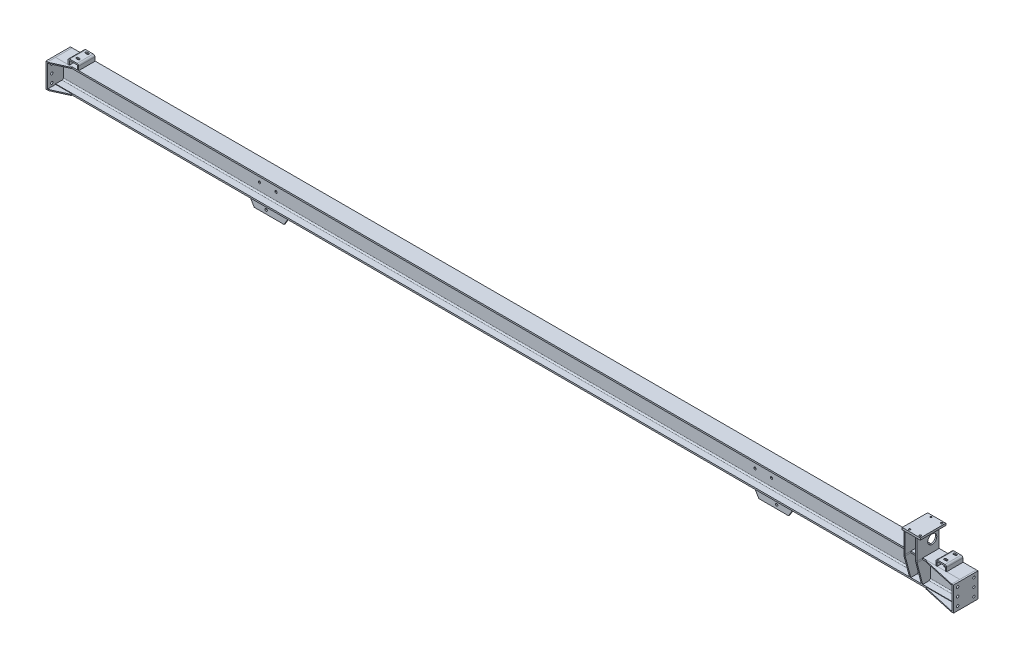
SolidWorks part; units mm, degrees
material "普通碳钢"
ref_plane "前视基准面" through (0, 0, 0) normal (0, 0, 1) x (1, 0, 0)
ref_plane "上视基准面" through (0, 0, 0) normal (0, 1, 0) x (1, 0, 0)
ref_plane "右视基准面" through (0, 0, 0) normal (1, 0, 0) x (0, 0, -1)
sketch "草图17" plane through (0, -1296.9389, 0) normal (0, 0, 1) x (1, 0, 0)
  line L0 (4200.9132, -4872.6106) -> (-1274.0868, -4872.6106)
  dimension "D1" = 5475
other "H型钢 HM150×100(3)"
ref_plane "基准面7" through (4200.9132, -6243.5496, 50) normal (-1, 0, 0) x (0, 0, 1)
sketch "草图1" plane through (4200.9132, -6243.5496, 50) normal (-1, 0, 0) x (0, 0, 1)
  line L0 (-50, -74) -> (50, -74)
  line L1 (50, -74) -> (50, -65)
  line L2 (50, -65) -> (11, -65)
  line L3 (3, -57) -> (3, 57)
  line L4 (11, 65) -> (50, 65)
  line L5 (50, 65) -> (50, 74)
  line L6 (50, 74) -> (-50, 74)
  line L7 (0, 74) -> (0, -74) construction
  line L11 (0, 60) -> (0, 74) construction
  line L14 (-50, -74) -> (-50, -65)
  line L15 (-50, -65) -> (-11, -65)
  line L16 (-3, -57) -> (-3, 57)
  line L17 (-11, 65) -> (-50, 65)
  line L18 (-50, 65) -> (-50, 74)
  arc A2 (11, -65) -> (3, -57) centre (11, -57) cw
  arc A3 (3, 57) -> (11, 65) centre (11, 57) cw
  arc A5 (-11, -65) -> (-3, -57) centre (-11, -57) ccw
  arc A6 (-3, 57) -> (-11, 65) centre (-11, 57) ccw
  point P2 (0, 0)
  point P38 (0, 0)
  point P39 (50, 74)
  point P40 (50, -74)
  point P41 (-50, -74)
  dimension "D8" = 8
  dimension "D1" = 6
  dimension "D2" = 9
  dimension "D3" = 148
  dimension "D4" = 100
  dimension "D9" = 0
sketch "草图18" plane through (4200.9132, 0, 0) normal (1, 0, 0) x (0, 0, -1)
  line L0 (0, -6317.5496) -> (-100, -6317.5496) construction
  line L1 (0, -6169.5496) -> (-148, -6169.5496)
  line L2 (0, -6169.5496) -> (0, -6317.5496)
  line L3 (0, -6317.5496) -> (-148, -6317.5496)
  line L4 (-148, -6169.5496) -> (-148, -6317.5496)
  dimension "D1" = 148
extrude "凸台-拉伸1" add sketch "草图18" along normal blind 10 separate body contours L1 L4 L3 L2
sketch "草图19" plane through (-1274.0868, 0, 0) normal (-1, 0, 0) x (0, 0, 1)
  line L0 (0, -6317.5496) -> (100, -6317.5496) construction
  line L1 (0, -6169.5496) -> (148, -6169.5496)
  line L2 (0, -6169.5496) -> (0, -6317.5496)
  line L3 (0, -6317.5496) -> (148, -6317.5496)
  line L4 (148, -6169.5496) -> (148, -6317.5496)
  dimension "D1" = 148
extrude "凸台-拉伸2" add sketch "草图19" along normal blind 10 separate body
sketch "草图20" plane through (0, -6169.5496, 0) normal (0, 1, 0) x (1, 0, 0)
  line L0 (-1274.0868, -100) -> (-1274.0868, -148)
  line L1 (-1274.0868, -148) -> (-1269.0868, -148)
  line L2 (-1269.0868, -148) -> (-1174.0868, -105)
  line L3 (-1174.0868, -105) -> (-1174.0868, -100)
  line L4 (-1274.0868, -100) -> (4200.9132, -100) construction
  line L5 (-1174.0868, -100) -> (-1274.0868, -100)
  dimension "D1" = 5
  dimension "D2" = 5
  dimension "D3" = 100
extrude "凸台-拉伸3" add sketch "草图20" against normal blind 6 separate body contours L2 L3 L5 L0 L1
sketch "草图21" plane through (0, -6317.5496, 0) normal (0, -1, 0) x (1, 0, 0)
  line L5 (-1269.0868, 148) -> (-1274.0868, 148)
  line L6 (-1274.0868, 148) -> (-1274.0868, 100)
  line L7 (-1274.0868, 100) -> (-1174.0868, 100)
  line L8 (-1174.0868, 100) -> (-1174.0868, 105)
  line L9 (-1174.0868, 105) -> (-1269.0868, 148)
  line L10 (-1269.0868, 148) -> (-1274.0868, 148)
  line L11 (-1274.0868, 148) -> (-1274.0868, 100)
  line L12 (-1274.0868, 100) -> (-1174.0868, 100)
  line L13 (-1174.0868, 100) -> (-1174.0868, 105)
  line L14 (-1174.0868, 105) -> (-1269.0868, 148)
  dimension "D1" = 0
extrude "凸台-拉伸4" add sketch "草图21" against normal blind 6 separate body
sketch "草图22" plane through (0, -6169.5496, 0) normal (0, 1, 0) x (1, 0, 0)
  line L0 (4200.9132, -100) -> (4200.9132, -148)
  line L1 (4200.9132, -148) -> (4195.9132, -148)
  line L2 (4195.9132, -148) -> (4000.9132, -105)
  line L3 (4000.9132, -105) -> (4000.9132, -100)
  line L4 (-1274.0868, -100) -> (4200.9132, -100) construction
  line L5 (4000.9132, -100) -> (4200.9132, -100)
  dimension "D1" = 200
  dimension "D2" = 5
  dimension "D3" = 5
extrude "凸台-拉伸5" add sketch "草图22" against normal blind 6 separate body contours L2 L3 L5 L0 L1
sketch "草图23" plane through (0, -6317.5496, 0) normal (0, -1, 0) x (1, 0, 0)
  line L5 (4200.9132, 148) -> (4195.9132, 148)
  line L6 (4195.9132, 148) -> (4000.9132, 105)
  line L7 (4000.9132, 105) -> (4000.9132, 100)
  line L8 (4000.9132, 100) -> (4200.9132, 100)
  line L9 (4200.9132, 100) -> (4200.9132, 148)
  line L10 (4200.9132, 148) -> (4195.9132, 148)
  line L11 (4195.9132, 148) -> (4000.9132, 105)
  line L12 (4000.9132, 105) -> (4000.9132, 100)
  line L13 (4000.9132, 100) -> (4200.9132, 100)
  line L14 (4200.9132, 100) -> (4200.9132, 148)
  dimension "D1" = 0
extrude "凸台-拉伸6" add sketch "草图23" against normal blind 6 separate body
sketch "草图24" plane through (-1284.0868, 0, 0) normal (-1, 0, 0) x (0, 0, 1)
  line L0 (0, -6242.5496) -> (148, -6242.5496) construction
  line L1 (0, -6169.5496) -> (0, -6317.5496) construction
  line L2 (148, -6317.5496) -> (148, -6169.5496) construction
  line L3 (0, -6192.5496) -> (148, -6192.5496) construction
  line L4 (0, -6292.5496) -> (148, -6292.5496) construction
  line L5 (25, -6169.5496) -> (25, -6317.5496) construction
  line L6 (148, -6169.5496) -> (0, -6169.5496) construction
  line L7 (0, -6317.5496) -> (148, -6317.5496) construction
  line L8 (123, -6169.5496) -> (123, -6317.5496) construction
  circle A0 centre (25, -6192.5496) radius 7
  circle A1 centre (123, -6192.5496) radius 7
  circle A2 centre (25, -6242.5496) radius 7
  circle A3 centre (123, -6242.5496) radius 7
  circle A4 centre (25, -6292.5496) radius 7
  circle A5 centre (123, -6292.5496) radius 7
  dimension "D5" = 14
  dimension "D1" = 50
  dimension "D2" = 50
  dimension "D3" = 25
  dimension "D4" = 25
  dimension "D6" = 25
extrude "切除-拉伸1" cut sketch "草图24" against normal up to next (10 mm away)
sketch "草图25" plane through (4210.9132, 0, 0) normal (1, 0, 0) x (0, 0, -1)
  line L0 (-148, -6242.5496) -> (0, -6242.5496) construction
  line L1 (-148, -6169.5496) -> (-148, -6317.5496) construction
  line L2 (0, -6169.5496) -> (0, -6317.5496) construction
  line L3 (-148, -6192.5496) -> (0, -6192.5496) construction
  line L4 (-148, -6292.5496) -> (0, -6292.5496) construction
  line L5 (-123, -6169.5496) -> (-123, -6317.5496) construction
  line L6 (0, -6169.5496) -> (-148, -6169.5496) construction
  line L7 (0, -6317.5496) -> (-148, -6317.5496) construction
  line L8 (-25, -6169.5496) -> (-25, -6317.5496) construction
  circle A0 centre (-123, -6192.5496) radius 7
  circle A1 centre (-25, -6192.5496) radius 7
  circle A2 centre (-123, -6242.5496) radius 7
  circle A3 centre (-25, -6242.5496) radius 7
  circle A4 centre (-123, -6292.5496) radius 7
  circle A5 centre (-25, -6292.5496) radius 7
  dimension "D5" = 14
  dimension "D1" = 25
  dimension "D2" = 25
  dimension "D3" = 50
  dimension "D4" = 50
  dimension "D6" = 25
extrude "切除-拉伸2" cut sketch "草图25" against normal up to next (10 mm away)
sketch "草图26" plane through (0, 0, 47) normal (0, 0, -1) x (-1, 0, 0)
  line L0 (-1463.4132, -6169.5496) -> (-1463.4132, -6909.0666) construction
  line L1 (-4200.9132, -6169.5496) -> (1274.0868, -6169.5496) construction
  line L2 (-2963.4132, -6169.5496) -> (-2963.4132, -6909.0666) construction
  line L3 (36.5868, -6169.5496) -> (36.5868, -6909.0666) construction
  line L4 (-3013.4132, -6169.5496) -> (-3013.4132, -6909.0666) construction
  line L5 (-2913.4132, -6169.5496) -> (-2913.4132, -6909.0666) construction
  line L6 (-13.4132, -6169.5496) -> (-13.4132, -6909.0666) construction
  line L7 (86.5868, -6169.5496) -> (86.5868, -6909.0666) construction
  line L10 (-4200.9132, -6254.5496) -> (1274.0868, -6254.5496) construction
  line L11 (-4200.9132, -6204.5496) -> (1274.0868, -6204.5496)
  line L12 (-4200.9132, -6204.5496) -> (1274.0868, -6204.5496) construction
  circle A0 centre (-3013.4132, -6204.5496) radius 7
  circle A1 centre (-2913.4132, -6204.5496) radius 7
  circle A2 centre (-13.4132, -6204.5496) radius 7
  circle A3 centre (86.5868, -6204.5496) radius 7
  circle A4 centre (-3013.4132, -6254.5496) radius 7
  circle A5 centre (-2913.4132, -6254.5496) radius 7
  circle A6 centre (-13.4132, -6254.5496) radius 7
  circle A7 centre (86.5868, -6254.5496) radius 7
  dimension "D8" = 14
  dimension "D1" = 1500
  dimension "D2" = 1500
  dimension "D3" = 50
  dimension "D4" = 50
  dimension "D5" = 50
  dimension "D6" = 50
  dimension "D7" = 35
  dimension "D9" = 50
extrude "切除-拉伸3" cut sketch "草图26" against normal up to next (6 mm away) and the other way through all
ref_plane "基准面8" through (0, -6039.5496, 0) normal (0, 1, 0) x (1, 0, 0)
sketch "草图27" plane through (0, -6039.5496, 0) normal (0, 1, 0) x (1, 0, 0)
  line L0 (4005.9132, -67) -> (3895.9132, -67) construction
  line L1 (4005.9132, 10) -> (3895.9132, 10)
  line L2 (4005.9132, 10) -> (4005.9132, -144)
  line L3 (4005.9132, -144) -> (3895.9132, -144)
  line L4 (3895.9132, 10) -> (3895.9132, -144)
  line L5 (3960.9132, -144) -> (3960.9132, 10) construction
  line L6 (3993.4132, -144) -> (3993.4132, 10) construction
  line L7 (3928.4132, -144) -> (3928.4132, 10) construction
  line L8 (4005.9132, -2) -> (3895.9132, -2) construction
  line L9 (4005.9132, -132) -> (3895.9132, -132) construction
  line L10 (4200.9132, 0) -> (-1274.0868, 0) construction
  line L11 (4200.9132, 0) -> (4200.9132, -148) construction
  circle A0 centre (3993.4132, -132) radius 5.5
  circle A1 centre (3928.4132, -132) radius 5.5
  circle A2 centre (3993.4132, -2) radius 5.5
  circle A3 centre (3928.4132, -2) radius 5.5
  dimension "D7" = 11
  dimension "D1" = 110
  dimension "D2" = 154
  dimension "D3" = 32.5
  dimension "D8" = 10
  dimension "D9" = 195
  dimension "D10" = 45
  dimension "D4" = 32.5
  dimension "D5" = 65
  dimension "D6" = 65
extrude "凸台-拉伸7" add sketch "草图27" along normal blind 12 separate body
sketch "草图29" plane through (0, -6039.5496, 0) normal (0, -1, 0) x (1, 0, 0)
  line L1 (3895.9132, 134) -> (3903.9132, 134)
  line L2 (3895.9132, 134) -> (3895.9132, 0)
  line L3 (3895.9132, 0) -> (3903.9132, 0)
  line L4 (3903.9132, 134) -> (3903.9132, 0)
  line L6 (3895.9132, -10) -> (3895.9132, 144) construction
  line L7 (3967.9132, 134) -> (3975.9132, 134)
  line L8 (3967.9132, 134) -> (3967.9132, 0)
  line L9 (3967.9132, 0) -> (3975.9132, 0)
  line L10 (3975.9132, 134) -> (3975.9132, 0)
  line L11 (4005.9132, -10) -> (3895.9132, -10) construction
  line L12 (3895.9132, 144) -> (4005.9132, 144) construction
  line L13 (4005.9132, 144) -> (4005.9132, -10) construction
  dimension "D1" = 8
  dimension "D2" = 8
  dimension "D3" = 10
  dimension "D4" = 10
  dimension "D5" = 30
extrude "凸台-拉伸8" add sketch "草图29" along normal up to surface (130 mm away) separate body up to face at (1463.4132, -6169.5496, 50)
sketch "草图30" plane through (0, -6169.5496, 0) normal (0, -1, 0) x (1, 0, 0)
  line L0 (-1274.0868, 100) -> (4200.9132, 100) construction
  line L1 (3975.9132, 0) -> (3975.9132, 134) construction
  line L2 (3967.9132, 134) -> (3967.9132, 0) construction
  line L3 (3903.9132, 0) -> (3903.9132, 134) construction
  line L4 (3903.9132, 134) -> (3895.9132, 134)
  line L5 (3895.9132, 134) -> (3895.9132, 0)
  line L6 (3895.9132, 0) -> (3903.9132, 0)
  line L7 (3903.9132, 0) -> (3903.9132, 134)
  line L8 (3903.9132, 134) -> (3895.9132, 134)
  line L9 (3895.9132, 134) -> (3895.9132, 100)
  line L10 (3895.9132, 100) -> (3903.9132, 100)
  line L11 (3903.9132, 100) -> (3903.9132, 134)
  line L12 (3975.9132, 134) -> (3967.9132, 134)
  line L13 (3967.9132, 134) -> (3967.9132, 0)
  line L14 (3967.9132, 0) -> (3975.9132, 0)
  line L15 (3975.9132, 0) -> (3975.9132, 134)
  line L16 (3975.9132, 134) -> (3967.9132, 134)
  line L17 (3967.9132, 134) -> (3967.9132, 100)
  line L18 (3967.9132, 100) -> (3975.9132, 100)
  line L19 (3975.9132, 100) -> (3975.9132, 134)
  line L20 (3895.9132, 134) -> (3895.9132, 0) construction
  dimension "D1" = 0
  dimension "D2" = 0
extrude "凸台-拉伸9" add sketch "草图30" along normal up to surface (9 mm away) separate body up to face at (1463.4132, -6178.5496, 80.5)
sketch "草图31" plane through (3895.9132, 0, 0) normal (-1, 0, 0) x (0, 0, 1)
  line L0 (100, -6178.5496) -> (134, -6178.5496) construction
  line L1 (100, -6178.5496) -> (134, -6178.5496)
  line L2 (61, -6178.5496) -> (100, -6178.5496) construction
  line L3 (61, -6178.5496) -> (100, -6178.5496)
  line L4 (100, -6308.5496) -> (61, -6308.5496) construction
  line L5 (100, -6308.5496) -> (61, -6308.5496)
  line L6 (134, -6178.5496) -> (100, -6308.5496)
  line L7 (53, -6300.5496) -> (53, -6186.5496) construction
  line L8 (53, -6300.5496) -> (53, -6186.5496)
  line L9 (61, -6178.5496) -> (53, -6186.5496)
  line L10 (53, -6300.5496) -> (61, -6308.5496)
extrude "凸台-拉伸10" add sketch "草图31" against normal up to surface (8 mm away) separate body up to face at (3903.9132, -6104.5496, 67)
sketch "草图32" plane through (3975.9132, 0, 0) normal (1, 0, 0) x (0, 0, -1)
  line L6 (-61, -6178.5496) -> (-134, -6178.5496)
  line L7 (-134, -6178.5496) -> (-100, -6308.5496)
  line L8 (-100, -6308.5496) -> (-61, -6308.5496)
  line L9 (-61, -6308.5496) -> (-53, -6300.5496)
  line L10 (-53, -6300.5496) -> (-53, -6186.5496)
  line L11 (-53, -6186.5496) -> (-61, -6178.5496)
  line L12 (-61, -6178.5496) -> (-134, -6178.5496)
  line L13 (-134, -6178.5496) -> (-100, -6308.5496)
  line L14 (-100, -6308.5496) -> (-61, -6308.5496)
  line L15 (-61, -6308.5496) -> (-53, -6300.5496)
  line L16 (-53, -6300.5496) -> (-53, -6186.5496)
  line L17 (-53, -6186.5496) -> (-61, -6178.5496)
  dimension "D1" = 0
extrude "凸台-拉伸11" add sketch "草图32" against normal up to surface (8 mm away) separate body up to face at (3967.9132, -6104.5496, 67)
sketch "草图33" plane through (3895.9132, 0, 0) normal (-1, 0, 0) x (0, 0, 1)
  line L0 (0, -6169.5496) -> (0, -6039.5496) construction
  line L1 (134, -6169.5496) -> (0, -6169.5496) construction
  circle A0 centre (42, -6099.5496) radius 27.5
  dimension "D1" = 42
  dimension "D3" = 55
  dimension "D2" = 70
extrude "切除-拉伸4" cut sketch "草图33" against normal up to surface (80 mm away)
ref_plane "基准面9" through (0, 0, 67) normal (0, 0, -1) x (-1, 0, 0)
sketch "草图34" plane through (0, 0, 67) normal (0, 0, -1) x (-1, 0, 0)
  line L0 (-4200.9132, -6169.5496) -> (1274.0868, -6169.5496) construction
  line L1 (-4120.9132, -6169.5496) -> (-4112.9132, -6169.5496)
  line L2 (-4120.9132, -6169.5496) -> (-4120.9132, -6146.0496)
  line L3 (-4110.9132, -6136.0496) -> (-4065.9132, -6136.0496)
  line L4 (-4055.9132, -6169.5496) -> (-4055.9132, -6146.0496)
  line L5 (-3975.9132, -6169.5496) -> (-3975.9132, -6039.5496) construction
  line L6 (-4112.9132, -6169.5496) -> (-4112.9132, -6146.0496)
  line L7 (-4110.9132, -6144.0496) -> (-4065.9132, -6144.0496)
  line L8 (-4063.9132, -6169.5496) -> (-4063.9132, -6146.0496)
  line L10 (-4112.9132, -6161.5496) -> (-4063.9132, -6161.5496) construction
  line L11 (-4112.9132, -6161.5496) -> (-4112.9132, -6146.0496) construction
  line L12 (-4063.9132, -6161.5496) -> (-4063.9132, -6146.0496) construction
  line L13 (-4063.9132, -6169.5496) -> (-4055.9132, -6169.5496)
  line L15 (-4120.9132, -6169.5496) -> (-4055.9132, -6169.5496) construction
  arc A0 (-4065.9132, -6136.0496) -> (-4055.9132, -6146.0496) centre (-4065.9132, -6146.0496) cw
  arc A1 (-4120.9132, -6146.0496) -> (-4110.9132, -6136.0496) centre (-4110.9132, -6146.0496) cw
  arc A2 (-4112.9132, -6146.0496) -> (-4110.9132, -6144.0496) centre (-4110.9132, -6146.0496) cw
  arc A3 (-4065.9132, -6144.0496) -> (-4063.9132, -6146.0496) centre (-4065.9132, -6146.0496) cw
  point P10 (-4055.9132, -6136.0496)
  point P13 (-4120.9132, -6136.0496)
  dimension "D4" = 10
  dimension "D1" = 65
  dimension "D2" = 33.5
  dimension "D3" = 80
  dimension "D5" = 8
extrude "凸台-拉伸12" add sketch "草图34" along normal mid plane 130 separate body
sketch "草图35" plane through (0, -6136.0496, 0) normal (0, 1, 0) x (1, 0, 0)
  line L0 (4110.9132, -67) -> (4065.9132, -67) construction
  line L1 (4110.9132, -2) -> (4110.9132, -132) construction
  line L2 (4065.9132, -2) -> (4065.9132, -132) construction
  line L3 (4088.4132, -2) -> (4088.4132, -132) construction
  line L4 (4065.9132, -2) -> (4110.9132, -2) construction
  line L5 (4065.9132, -132) -> (4110.9132, -132) construction
  line L6 (4110.9132, -17) -> (4065.9132, -17) construction
  line L7 (4110.9132, -117) -> (4065.9132, -117) construction
  circle A0 centre (4088.4132, -17) radius 6
  circle A1 centre (4088.4132, -117) radius 6
  dimension "D3" = 12
  dimension "D4" = 12
  dimension "D1" = 50
  dimension "D2" = 50
sketch "草图36" plane through (0, 0, 67) normal (0, 0, -1) x (-1, 0, 0)
  line L0 (1284.0868, -6169.5496) -> (1284.0868, -6317.5496) construction
  line L1 (1134.0868, -6169.5496) -> (1142.0868, -6169.5496)
  line L2 (1134.0868, -6169.5496) -> (1134.0868, -6146.0496)
  line L3 (1144.0868, -6136.0496) -> (1189.0868, -6136.0496)
  line L4 (1199.0868, -6169.5496) -> (1199.0868, -6146.0496)
  line L5 (-4065.9132, -6136.0496) -> (-4110.9132, -6136.0496) construction
  line L6 (-4200.9132, -6169.5496) -> (1274.0868, -6169.5496) construction
  line L7 (1142.0868, -6169.5496) -> (1142.0868, -6146.0496)
  line L8 (1144.0868, -6144.0496) -> (1189.0868, -6144.0496)
  line L9 (1191.0868, -6169.5496) -> (1191.0868, -6146.0496)
  line L11 (1142.0868, -6161.5496) -> (1191.0868, -6161.5496) construction
  line L12 (1142.0868, -6161.5496) -> (1142.0868, -6146.0496) construction
  line L13 (1191.0868, -6161.5496) -> (1191.0868, -6146.0496) construction
  line L14 (1191.0868, -6169.5496) -> (1199.0868, -6169.5496)
  line L16 (1134.0868, -6169.5496) -> (1199.0868, -6169.5496) construction
  arc A0 (1189.0868, -6136.0496) -> (1199.0868, -6146.0496) centre (1189.0868, -6146.0496) cw
  arc A1 (1134.0868, -6146.0496) -> (1144.0868, -6136.0496) centre (1144.0868, -6146.0496) cw
  arc A2 (1142.0868, -6146.0496) -> (1144.0868, -6144.0496) centre (1144.0868, -6146.0496) cw
  arc A3 (1189.0868, -6144.0496) -> (1191.0868, -6146.0496) centre (1189.0868, -6146.0496) cw
  point P12 (1199.0868, -6136.0496)
  point P15 (1134.0868, -6136.0496)
  dimension "D3" = 10
  dimension "D1" = 85
  dimension "D2" = 65
  dimension "D4" = 8
extrude "凸台-拉伸13" add sketch "草图36" along normal mid plane 130 separate body
sketch "草图38" plane through (0, -6317.5496, 0) normal (0, -1, 0) x (1, 0, 0)
  line L0 (-1274.0868, 0) -> (4200.9132, 0) construction
  line L1 (3140.9132, 17) -> (2840.9132, 17)
  line L2 (3140.9132, 17) -> (3140.9132, 9)
  line L3 (3140.9132, 9) -> (2840.9132, 9)
  line L4 (2840.9132, 17) -> (2840.9132, 9)
  line L5 (4210.9132, 0) -> (4210.9132, 148) construction
  dimension "D1" = 9
  dimension "D2" = 8
  dimension "D3" = 300
  dimension "D4" = 1070
extrude "凸台-拉伸14" add sketch "草图38" along normal blind 120 separate body
chamfer "倒角1" distance 100 distance2 60 1 edges at (2840.9132, -6437.5496, 13)
chamfer "倒角2" distance 100 distance2 60 1 edges at (3140.9132, -6437.5496, 13)
sketch "草图39" plane through (0, 0, 17) normal (0, 0, 1) x (1, 0, 0)
  line L0 (2840.9132, -6317.5496) -> (3140.9132, -6317.5496) construction
  line L1 (2962.9132, -6350.0496) -> (3008.7994, -6415.5817) construction
  line L2 (2900.9132, -6437.5496) -> (3080.9132, -6437.5496) construction
  line L3 (2840.9132, -6337.5496) -> (2840.9132, -6317.5496) construction
  circle A0 centre (2962.9132, -6350.0496) radius 7
  circle A1 centre (3008.7994, -6415.5817) radius 7
  dimension "D1" = 32.5
  dimension "D5" = 14
  dimension "D6" = 14
  dimension "D2" = 55
  dimension "D3" = 80
  dimension "D4" = 122
extrude "切除-拉伸7" cut sketch "草图39" against normal up to next (8 mm away)
sketch "草图40" plane through (0, -6169.5496, 0) normal (0, 1, 0) x (1, 0, 0)
  line L0 (4120.9132, -132) -> (4112.9132, -132) construction
  line L1 (4120.9132, -132) -> (4055.9132, -132)
  line L2 (4120.9132, -132) -> (4120.9132, -100)
  line L3 (4120.9132, -100) -> (4055.9132, -100)
  line L4 (4055.9132, -132) -> (4055.9132, -100)
  line L5 (-1274.0868, -100) -> (4200.9132, -100) construction
  line L6 (4055.9132, -2) -> (4055.9132, -132) construction
  line L7 (4120.9132, -2) -> (4120.9132, -132) construction
extrude "切除-拉伸8" cut sketch "草图40" along normal up to surface (33.5 mm away) up to face at (4088.4132, -6136.0496, 67)
sketch "草图41" plane through (0, -6169.5496, 0) normal (0, 1, 0) x (1, 0, 0)
  line L0 (-1274.0868, -100) -> (4200.9132, -100) construction
  line L1 (-1199.0868, -132) -> (-1134.0868, -132)
  line L2 (-1199.0868, -132) -> (-1199.0868, -100)
  line L3 (-1199.0868, -100) -> (-1134.0868, -100)
  line L4 (-1134.0868, -132) -> (-1134.0868, -100)
  line L5 (-1134.0868, -2) -> (-1134.0868, -132) construction
  line L6 (-1199.0868, -2) -> (-1199.0868, -132) construction
  line L7 (-1191.0868, -132) -> (-1199.0868, -132) construction
extrude "切除-拉伸9" cut sketch "草图41" along normal up to surface (33.5 mm away) up to face at (-1166.5868, -6136.0496, 67)
sketch "草图42" plane through (0, -6317.5496, 0) normal (0, -1, 0) x (1, 0, 0)
  line L0 (-1274.0868, 0) -> (4200.9132, 0) construction
  line L1 (85.9132, 9) -> (-214.0868, 9)
  line L2 (85.9132, 9) -> (85.9132, 17)
  line L3 (85.9132, 17) -> (-214.0868, 17)
  line L4 (-214.0868, 9) -> (-214.0868, 17)
  line L5 (-1284.0868, 0) -> (-1284.0868, 148) construction
  dimension "D1" = 9
  dimension "D2" = 8
  dimension "D3" = 300
  dimension "D4" = 1070
extrude "凸台-拉伸15" add sketch "草图42" along normal blind 120 separate body
chamfer "倒角3" distance 100 distance2 60 1 edges at (85.9132, -6437.5496, 13)
chamfer "倒角4" distance 100 distance2 60 1 edges at (-214.0868, -6437.5496, 13)
sketch "草图43" plane through (0, 0, 17) normal (0, 0, 1) x (1, 0, 0)
  line L0 (-36.0868, -6350.0496) -> (-81.9729, -6415.5817) construction
  line L1 (-1274.0868, -6317.5496) -> (4200.9132, -6317.5496) construction
  line L3 (85.9132, -6337.5496) -> (85.9132, -6317.5496) construction
  circle A0 centre (-36.0868, -6350.0496) radius 7
  circle A1 centre (-81.9729, -6415.5817) radius 7
  dimension "D1" = 32.5
  dimension "D3" = 14
  dimension "D4" = 14
  dimension "D2" = 122
  dimension "D5" = 80
  dimension "D6" = 55
extrude "切除-拉伸10" cut sketch "草图43" against normal up to next (8 mm away)
sketch "草图44" plane through (0, -6136.0496, 0) normal (0, 1, 0) x (1, 0, 0)
  line L0 (4088.4132, -2) -> (4088.4132, -100) construction
  line L1 (4065.9132, -2) -> (4110.9132, -2) construction
  line L2 (4065.9132, -100) -> (4110.9132, -100) construction
  line L3 (4065.9132, -16) -> (4110.9132, -16) construction
  line L4 (4065.9132, -2) -> (4065.9132, -100) construction
  line L5 (4110.9132, -2) -> (4110.9132, -100) construction
  line L6 (4065.9132, -72) -> (4110.9132, -72) construction
  line L7 (4083.4132, -16) -> (4083.4132, -72) construction
  line L8 (4093.4132, -16) -> (4093.4132, -72) construction
  line L9 (4083.4132, -10) -> (4093.4132, -10)
  line L10 (4083.4132, -22) -> (4093.4132, -22)
  line L11 (4083.4132, -66) -> (4093.4132, -66)
  line L12 (4083.4132, -78) -> (4093.4132, -78)
  arc A0 (4083.4132, -10) -> (4083.4132, -22) centre (4083.4132, -16) ccw
  arc A1 (4093.4132, -22) -> (4093.4132, -10) centre (4093.4132, -16) ccw
  arc A2 (4083.4132, -66) -> (4083.4132, -78) centre (4083.4132, -72) ccw
  arc A3 (4093.4132, -78) -> (4093.4132, -66) centre (4093.4132, -72) ccw
  dimension "D5" = 12
  dimension "D1" = 14
  dimension "D2" = 56
  dimension "D3" = 5
  dimension "D4" = 5
extrude "切除-拉伸11" cut sketch "草图44" against normal up to next (8 mm away)
sketch "草图45" plane through (0, -6169.5496, 0) normal (0, 1, 0) x (1, 0, 0)
  line L0 (4088.4132, -2) -> (4088.4132, -100) construction
  line L1 (4065.9132, -2) -> (4110.9132, -2) construction
  line L2 (4065.9132, -100) -> (4110.9132, -100) construction
  line L3 (-1274.0868, 0) -> (4200.9132, 0) construction
  circle A0 centre (4088.4132, -16) radius 9
  circle A1 centre (4088.4132, -72) radius 9
  dimension "D1" = 18
  dimension "D2" = 16
  dimension "D3" = 56
extrude "切除-拉伸12" cut sketch "草图45" against normal up to next (9 mm away)
sketch "草图46" plane through (0, -6136.0496, 0) normal (0, 1, 0) x (1, 0, 0)
  line L0 (-1166.5868, -100) -> (-1166.5868, -2) construction
  line L1 (-1189.0868, -100) -> (-1144.0868, -100) construction
  line L2 (-1189.0868, -2) -> (-1144.0868, -2) construction
  line L3 (-1144.0868, -16) -> (-1189.0868, -16) construction
  line L4 (-1144.0868, -2) -> (-1144.0868, -100) construction
  line L5 (-1189.0868, -2) -> (-1189.0868, -100) construction
  line L6 (-1144.0868, -72) -> (-1189.0868, -72) construction
  line L7 (-1161.5868, -72) -> (-1161.5868, -16) construction
  line L8 (-1171.5868, -72) -> (-1171.5868, -16) construction
  line L9 (-1161.5868, -78) -> (-1171.5868, -78)
  line L11 (-1161.5868, -66) -> (-1171.5868, -66)
  line L15 (-1161.5868, -10) -> (-1171.5868, -10)
  line L17 (-1171.5868, -22) -> (-1161.5868, -22)
  arc A0 (-1161.5868, -78) -> (-1161.5868, -66) centre (-1161.5868, -72) ccw
  arc A1 (-1171.5868, -66) -> (-1171.5868, -78) centre (-1171.5868, -72) ccw
  arc A2 (-1161.5868, -22) -> (-1161.5868, -10) centre (-1161.5868, -16) ccw
  arc A3 (-1171.5868, -10) -> (-1171.5868, -22) centre (-1171.5868, -16) ccw
  dimension "D5" = 12
  dimension "D1" = 56
  dimension "D2" = 14
  dimension "D3" = 5
  dimension "D4" = 5
extrude "切除-拉伸13" cut sketch "草图46" against normal up to next (8 mm away)
ref_plane "基准面10" through (2965.9132, 0, 0) normal (-1, 0, 0) x (0, 0, 1)
sketch "草图49" plane through (2965.9132, 0, 0) normal (-1, 0, 0) x (0, 0, 1)
  line L0 (47, -6186.5496) -> (47, -6300.5496) construction
  line L1 (47, -6188.5496) -> (47, -6298.5496)
  line L2 (0, -6178.5496) -> (39, -6178.5496) construction
  line L3 (2, -6178.5496) -> (37, -6178.5496)
  line L4 (2, -6186.5496) -> (2, -6300.5496) construction
  line L5 (47, -6186.5496) -> (47, -6300.5496) construction
  line L7 (37, -6178.5496) -> (47, -6188.5496)
  line L12 (39, -6308.5496) -> (0, -6308.5496) construction
  line L13 (37, -6308.5496) -> (2, -6308.5496)
  line L14 (2, -6178.5496) -> (2, -6308.5496)
  line L15 (47, -6298.5496) -> (37, -6308.5496)
  point P12 (47, -6178.5496)
  point P15 (47, -6178.5496)
  point P18 (47, -6308.5496)
  dimension "D2" = 45
extrude "凸台-拉伸18" add sketch "草图49" along normal blind 6 separate body
